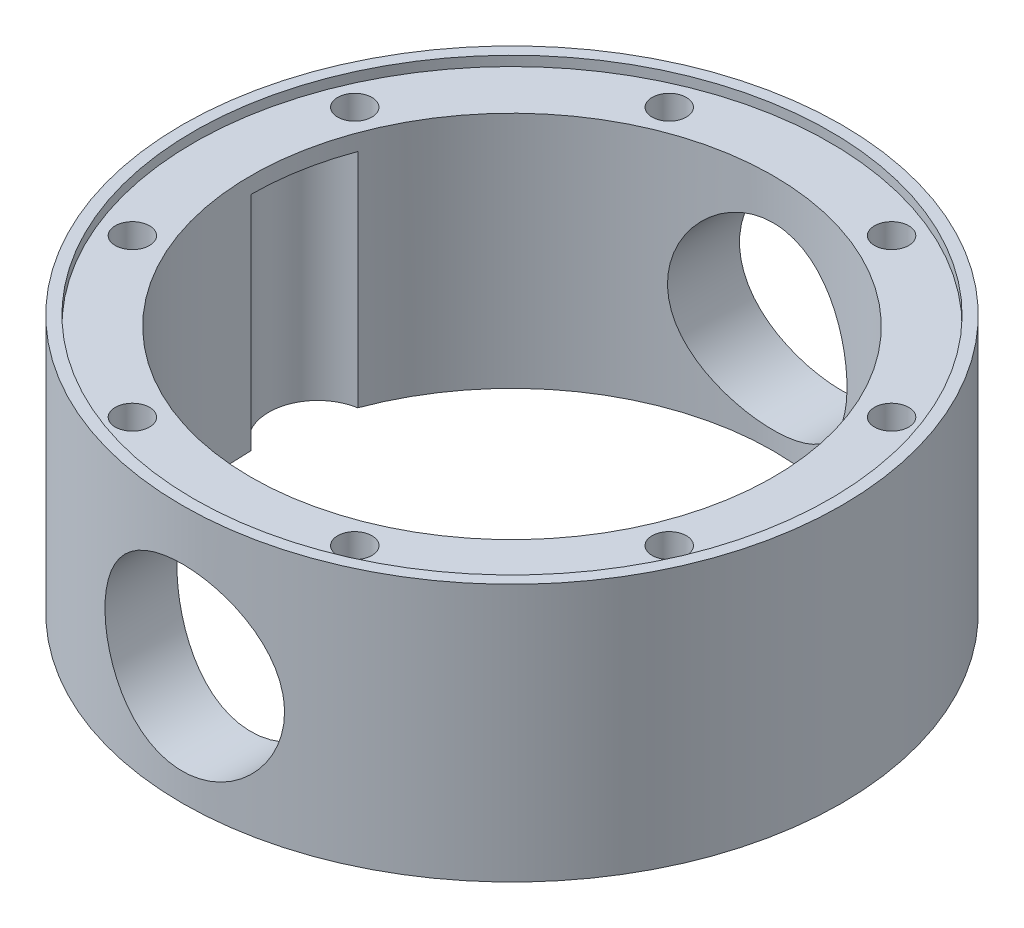
SolidWorks part; units mm, degrees
material "1.0037 (S235JR)"
ref_plane "Front Plane" through (0, 0, 0) normal (0, 0, 1) x (1, 0, 0)
ref_plane "Top Plane" through (0, 0, 0) normal (0, 1, 0) x (1, 0, 0)
ref_plane "Right Plane" through (0, 0, 0) normal (1, 0, 0) x (0, 0, -1)
sketch "Sketch1" plane through (0, 0, 0) normal (0, 1, 0) x (1, 0, 0)
  circle A0 centre (0, 0) radius 101
  circle A1 centre (0, 0) radius 80
  dimension "D1" = 202
  dimension "D2" = 160
extrude "Boss-Extrude1" add sketch "Sketch1" along normal mid plane 76
sketch "Sketch3" plane through (0, 0, 0) normal (0, 0, 1) x (1, 0, 0)
  line L0 (-101, -38) -> (101, -38) construction
  line L1 (0, -5) -> (100.02, -5) construction
  line L3 (0, -5) -> (-100.02, -5) construction
  circle A0 centre (0, -5) radius 27.5
  dimension "D1" = 55
  dimension "D2" = 33
extrude "Cut-Extrude1" cut sketch "Sketch3" against normal through all both and the other way through all
sketch "Sketch4" plane through (0, 38, 0) normal (0, 1, 0) x (1, 0, 0)
  line L0 (-34.0588, 82.2253) -> (0, 0) construction
  line L1 (0, 0) -> (0, 98.5773) construction
  circle A0 centre (-34.0588, 82.2253) radius 5.25
  dimension "D1" = 10.5
  dimension "D2" = 89
  dimension "D3" = 22.5
extrude "Cut-Extrude2" cut sketch "Sketch4" against normal up to next (76 mm away)
pattern_circular "CirPattern1" count 8 over 360 about axis through (0, 0, 0) along (0, 1, 0) of "Cut-Extrude2"
sketch "Sketch5" plane through (0, -38, 0) normal (0, -1, 0) x (1, 0, 0)
  line L0 (0, 0) -> (0, 2) construction
  line L1 (-72.5, 2) -> (-72.5, -28) construction
  line L2 (-72.5, 2) -> (72.5, 2)
  line L3 (72.5, 2) -> (72.5, -28) construction
  line L4 (-72.5, -28) -> (72.5, -28)
  arc A0 (-72.5, 2) -> (-72.5, -28) centre (-72.5, -13) ccw
  arc A1 (72.5, 2) -> (72.5, -28) centre (72.5, -13) cw
  dimension "D1" = 2
  dimension "D2" = 145
  dimension "D3" = 30
extrude "Cut-Extrude3" cut sketch "Sketch5" against normal blind 68
sketch "Sketch6" plane through (0, -38, 0) normal (0, -1, 0) x (1, 0, 0)
  circle A0 centre (0, 0) radius 101 construction
  circle A1 centre (0, 0) radius 101
  circle A2 centre (0, 0) radius 97.5
  dimension "D1" = 195
extrude "Boss-Extrude2" add sketch "Sketch6" along normal blind 3
sketch "Sketch7" plane through (0, 38, 0) normal (0, 1, 0) x (1, 0, 0)
  circle A2 centre (0, 0) radius 97.5
  circle A3 centre (0, 0) radius 97.5
  dimension "D1" = 0
extrude "Cut-Extrude4" cut sketch "Sketch7" against normal blind 3
